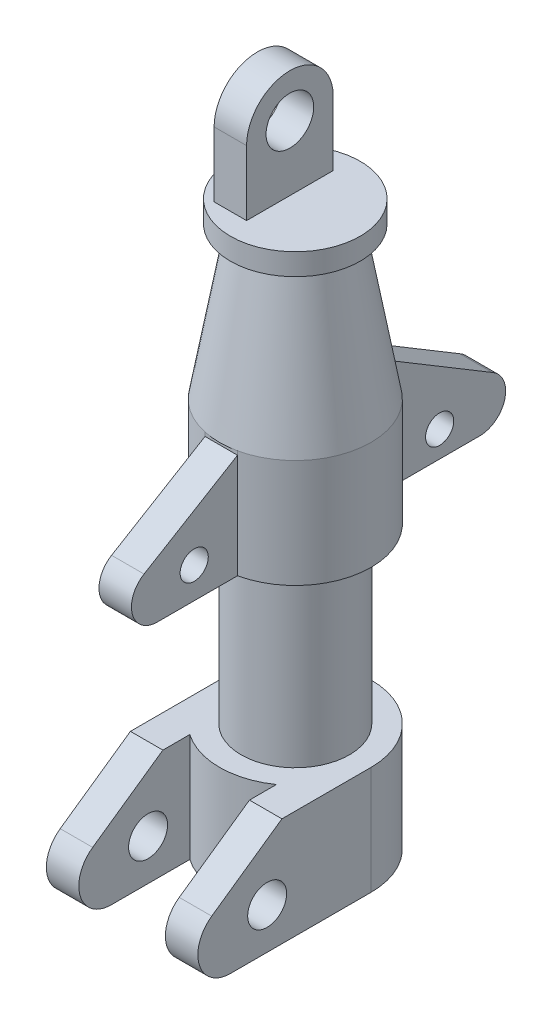
SolidWorks part; units mm, degrees
material "AISI 304"
ref_plane "Front Plane" through (0, 0, 0) normal (0, 0, 1) x (1, 0, 0)
ref_plane "Top Plane" through (0, 0, 0) normal (0, 1, 0) x (1, 0, 0)
ref_plane "Right Plane" through (0, 0, 0) normal (1, 0, 0) x (0, 0, -1)
sketch "Sketch1" plane through (0, 0, 0) normal (0, 0, 1) x (1, 0, 0)
  line L0 (0, 462.1484) -> (0, -240.0305) construction
  line L1 (0, 260) -> (30, 260)
  line L2 (30, 260) -> (30, 250)
  line L3 (30, 250) -> (22.6571, 250)
  line L4 (22.6571, 250) -> (35, 180)
  line L5 (35, 180) -> (35, 130)
  line L6 (35, 130) -> (25, 130)
  line L7 (25, 130) -> (25, 50)
  line L8 (25, 50) -> (35, 50)
  line L9 (35, 50) -> (35, 0)
  line L10 (35, 0) -> (0, 0)
  line L11 (0, 260) -> (0, 0)
  point P23 (35, 155)
  dimension "D1" = 30
  dimension "D2" = 10
  dimension "D3" = 70
  dimension "D4" = 50
  dimension "D5" = 80
  dimension "D6" = 50
  dimension "D7" = 35
  dimension "D8" = 25
  dimension "D9" = 35
  dimension "D10" = 10
revolve "Revolve1" add sketch "Sketch1" angle 360 about L0
sketch "Sketch2" plane through (0, 0, 0) normal (0, 1, 0) x (1, 0, 0)
  line L0 (0, 63.7444) -> (0, -125.6183) construction
  line L1 (-62.0947, 0) -> (67.939, 0) construction
  line L2 (-35, 0) -> (-35, -93.1949)
  line L3 (-35, -93.1949) -> (-20, -93.1949)
  line L4 (-20, -93.1949) -> (-20, 0)
  line L5 (-20, 0) -> (-35, 0)
  line L6 (35, -93.1949) -> (20, -93.1949)
  line L7 (20, -93.1949) -> (20, 0)
  line L8 (20, 0) -> (35, 0)
  line L9 (35, 0) -> (35, -93.1949)
  circle A0 centre (0, 0) radius 35 construction
  dimension "D1" = 15
extrude "Boss-Extrude2" add sketch "Sketch2" along normal up to surface (50 mm away) up to face at (0, 50, 25)
sketch "Sketch3" plane through (-35, 0, 0) normal (-1, 0, 0) x (0, 0, 1)
  line L0 (0, 50) -> (0, 0) construction
  line L1 (0, 0) -> (93.1949, 0) construction
  line L2 (73.6036, 27.2873) -> (41.1665, 50)
  line L6 (93.1949, 50) -> (0, 50) construction
  line L7 (41.1665, 50) -> (93.1949, 50)
  line L8 (93.1949, 50) -> (93.1949, 0)
  line L9 (93.1949, 0) -> (65, 0)
  circle A0 centre (48, 19) radius 9
  arc A1 (65, 0) -> (73.6036, 27.2873) centre (65, 15) ccw
  dimension "D1" = 18
  dimension "D4" = 30
  dimension "D6" = 35
  dimension "D2" = 48
  dimension "D3" = 19
  dimension "D5" = 17
extrude "Cut-Extrude6" cut sketch "Sketch3" against normal blind 105
sketch "Sketch4" plane through (0, 0, 0) normal (0, 1, 0) x (1, 0, 0)
  line L0 (0, 123.2303) -> (0, -174.8786) construction
  line L1 (-114.0346, 0) -> (195.8392, 0) construction
ref_plane "Plane1" through (0, 180, 0) normal (0, 1, 0) x (1, 0, 0)
sketch "Sketch6" plane through (0, 180, 0) normal (0, 1, 0) x (1, 0, 0)
  line L0 (0, 0) -> (7.5, 0)
  line L1 (7.5, 91.6629) -> (7.5, 9.2531)
  line L2 (7.5, -91.6629) -> (-7.5, -91.6629)
  line L3 (-7.5, -91.6629) -> (-7.5, 0)
  line L4 (-7.5, 0) -> (0, 0)
  line L5 (-94.8994, 0) -> (122.3459, 0) construction
  line L6 (0, -125.1828) -> (0, 159.397) construction
  line L7 (7.5, 91.6629) -> (-7.5, 91.6629)
  line L8 (-7.5, 9.9743) -> (7.5, 9.2531)
  line L9 (-7.5, 9.9743) -> (-7.5, 91.6629)
  line L10 (7.5, 0) -> (7.5, -91.6629)
  dimension "D1" = 7.5
  dimension "D2" = 15
extrude "Boss-Extrude4" add sketch "Sketch6" against normal up to surface (50 mm away) up to face at (0, 130, 35)
sketch "Sketch7" plane through (-7.5, 0, 0) normal (-1, 0, 0) x (0, 0, 1)
  line L0 (34.187, 130) -> (34.187, 180) construction
  line L1 (91.6629, 130) -> (34.187, 130) construction
  line L2 (31.2436, 180) -> (77.3674, 152.286)
  line L3 (170.4306, 180) -> (-170.4306, 180) construction
  line L4 (71.187, 130) -> (91.6629, 130)
  line L5 (91.6629, 130) -> (91.6629, 180)
  line L6 (-34.187, 180) -> (-34.187, 130) construction
  line L7 (-34.187, 130) -> (-91.6629, 130) construction
  line L8 (-91.6629, 180) -> (-37.7314, 180)
  line L9 (-34.187, 180) -> (34.187, 180) construction
  line L10 (-37.7314, 180) -> (-91.6629, 180)
  line L11 (-91.6629, 180) -> (-91.6629, 130)
  line L12 (-91.6629, 130) -> (-77.687, 130)
  line L13 (-83.5319, 152.4803) -> (-37.7314, 180)
  line L14 (31.2436, 180) -> (91.6629, 180)
  circle A0 centre (54.187, 144.29) radius 6.5
  circle A1 centre (-59.187, 142) radius 6.5
  arc A3 (-83.5319, 152.4803) -> (-77.687, 130) centre (-77.687, 142) ccw
  arc A4 (71.187, 130) -> (77.3674, 152.286) centre (71.187, 142) ccw
  line M4 (34.187, 180) -> (34.187, 130)
  line M5 (34.187, 130) -> (91.6629, 130)
  line M6 (91.6629, 130) -> (91.6629, 180)
  line M7 (91.6629, 180) -> (34.187, 180)
  dimension "D1" = 20
  dimension "D3" = 13
  dimension "D4" = 17
  dimension "D5" = 24
  dimension "D7" = 13
  dimension "D9" = 24
  dimension "D10" = 31
  dimension "D2" = 14.29
  dimension "D6" = 25
  dimension "D8" = 12
  dimension "D11" = 31
extrude "Cut-Extrude7" cut sketch "Sketch7" against normal blind 105 contours A3 L13 L8 L11 L12 | A4 L2 M5 M6 M7 M4 | A0 | A1
sketch "Sketch8" plane through (0, 0, 0) normal (0, -1, 0) x (1, 0, 0)
  circle A0 centre (0, 0) radius 20
  dimension "D1" = 40
extrude "Cut-Extrude8" cut sketch "Sketch8" against normal blind 235
sketch "Sketch11" plane through (0, 260, 0) normal (0, 1, 0) x (1, 0, 0)
  line L0 (0, 59.4859) -> (0, -72.8729) construction
  line L1 (-70.4882, 0) -> (110.0412, 0) construction
  line L2 (-2.5, 20) -> (-2.5, -20)
  line L3 (-2.5, -20) -> (-17.5, -20)
  line L4 (-17.5, -20) -> (-17.5, 20)
  line L5 (-17.5, 20) -> (-2.5, 20)
  dimension "D1" = 5
  dimension "D2" = 15
  dimension "D3" = 20
  dimension "D4" = 40
extrude "Boss-Extrude5" add sketch "Sketch11" along normal blind 60
sketch "Sketch12" plane through (-17.5, 0, 0) normal (-1, 0, 0) x (0, 0, 1)
  line L0 (-20, 260) -> (20, 260) construction
  line L1 (-20, 290) -> (-20, 320)
  line L2 (-20, 320) -> (20, 320)
  line L3 (20, 320) -> (20, 290)
  circle A0 centre (0, 290) radius 11
  arc A1 (20, 290) -> (-20, 290) centre (0, 290) ccw
  dimension "D1" = 40
  dimension "D2" = 22
  dimension "D3" = 30
  dimension "D4" = 30
extrude "Cut-Extrude9" cut sketch "Sketch12" against normal blind 60
